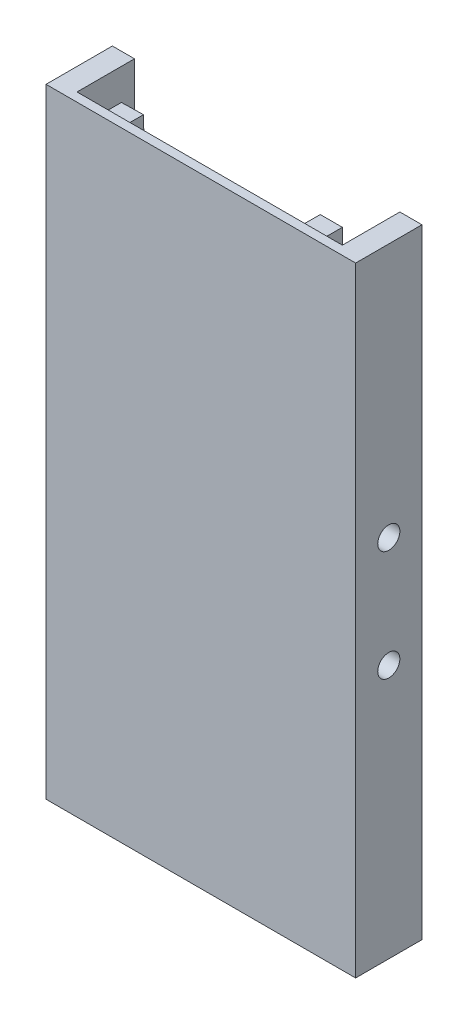
SolidWorks part; units mm, degrees
ref_plane "Front Plane" through (0, 0, 0) normal (0, 0, 1) x (1, 0, 0)
ref_plane "Top Plane" through (0, 0, 0) normal (0, 1, 0) x (1, 0, 0)
ref_plane "Right Plane" through (0, 0, 0) normal (1, 0, 0) x (0, 0, -1)
sketch "Sketch2" plane through (0, 0, 0) normal (0, 0, 1) x (1, 0, 0)
  line L0 (0, 438.8889) -> (0, 298.8889)
  line L1 (0, 298.8889) -> (70, 298.8889)
  line L2 (70, 298.8889) -> (70, 438.8889)
  line L4 (0, 438.8889) -> (70, 438.8889)
  dimension "D1" = 70
  dimension "D2" = 140
extrude "Boss-Extrude1" add sketch "Sketch2" against normal blind 15
sketch "Sketch3" plane through (0, 0, -15) normal (0, 0, -1) x (-1, 0, 0)
  line L0 (-65, 433.8889) -> (-65, 303.8889)
  line L1 (-65, 303.8889) -> (-5, 303.8889)
  line L2 (-5, 303.8889) -> (-5, 433.8889)
  line L4 (-65, 433.8889) -> (-5, 433.8889)
  line L5 (-70, 298.8889) -> (-70, 438.8889) construction
  line L6 (0, 438.8889) -> (0, 298.8889) construction
  line L7 (-70, 438.8889) -> (0, 438.8889) construction
  line L8 (0, 298.8889) -> (-70, 298.8889) construction
  dimension "D1" = 5
  dimension "D2" = 5
  dimension "D3" = 5
  dimension "D4" = 5
extrude "Cut-Extrude1" cut sketch "Sketch3" against normal blind 12.5
sketch "Sketch4" plane through (0, 438.8889, 0) normal (0, 1, 0) x (1, 0, 0)
  line L0 (5, 15) -> (5, 2)
  line L1 (5, 15) -> (65, 15)
  line L2 (65, 15) -> (65, 2)
  line L3 (65, 2) -> (5, 2)
  line L6 (70, 0) -> (0, 0) construction
  dimension "D1" = 2
extrude "Cut-Extrude2" cut sketch "Sketch4" against normal through all
sketch "Sketch7" plane through (0, 0, 0) normal (-1, 0, 0) x (0, 0, 1)
  line L0 (-7.5, 438.8889) -> (-7.5, 298.8889) construction
  line L1 (-15, 438.8889) -> (0, 438.8889) construction
  line L2 (-15, 298.8889) -> (0, 298.8889) construction
  line L3 (-25, 368.8889) -> (-15, 368.8889) construction
  line L4 (-15, 438.8889) -> (-15, 298.8889) construction
  circle A0 centre (-7.5, 381.3889) radius 2.5
  circle A1 centre (-7.5, 356.3889) radius 2.5
  dimension "D2" = 5
  dimension "D1" = 25
extrude "Cut-Extrude5" cut sketch "Sketch7" against normal through all
sketch "Sketch32" plane through (0, 298.8889, 0) normal (0, -1, 0) x (1, 0, 0)
  line L0 (35, -2) -> (35, 0) construction
  line L1 (5, -2) -> (65, -2) construction
  line L2 (0, 0) -> (70, 0) construction
  line L3 (33.5, -2) -> (36.5, -2)
  arc A0 (33.5, -2) -> (36.5, -2) centre (35, -2) cw
  dimension "D1" = 3
revolve "Cut-Revolve1" cut sketch "Sketch32" angle 30 about L3
ref_plane "Plane8" through (5, 0, 0) normal (1, 0, 0) x (0, 0, -1)
sketch "Sketch35" plane through (5, 0, 0) normal (1, 0, 0) x (0, 0, -1)
  circle A0 centre (7.5, 356.3889) radius 1
  dimension "D1" = 2
curve "Helix/Spiral6" pitch 1.5333 height 23 turns 15
ref_plane "Plane9" through (28, 355.6818, -8.2071) normal (0.2371, -0.6869, 0.6869) x (0.9715, 0.1676, -0.1676)
sketch "Sketch36" plane through (0, 0, -2) normal (0, 0, -1) x (-1, 0, 0)
  line L0 (-35, 438.8889) -> (-36.5, 298.8889) construction
  line L1 (-5, 438.8889) -> (-65, 438.8889) construction
  line L2 (-65, 368.8889) -> (-5, 368.8889) construction
  line L3 (-65, 438.8889) -> (-65, 298.8889) construction
  line L4 (-5, 298.8889) -> (-5, 438.8889) construction
  line L5 (-65, 298.8889) -> (-65, 438.8889) construction
  line L6 (-60, 437.3889) -> (-55, 437.3889)
  line L7 (-60, 437.3889) -> (-60, 432.3889)
  line L8 (-60, 432.3889) -> (-55, 432.3889)
  line L9 (-55, 437.3889) -> (-55, 432.3889)
  line L10 (-10.145, 431.8547) -> (-15.1439, 431.9619)
  line L11 (-10.0379, 436.8536) -> (-10.145, 431.8547)
  line L12 (-10.0379, 436.8536) -> (-15.0367, 436.9607)
  line L13 (-15.0367, 436.9607) -> (-15.1439, 431.9619)
  line L14 (-10.145, 305.923) -> (-15.1439, 305.8159)
  line L15 (-10.0379, 300.9242) -> (-10.145, 305.923)
  line L16 (-10.0379, 300.9242) -> (-15.0367, 300.8171)
  line L17 (-15.0367, 300.8171) -> (-15.1439, 305.8159)
  line L18 (-60, 305.3889) -> (-55, 305.3889)
  line L19 (-60, 300.3889) -> (-60, 305.3889)
  line L20 (-60, 300.3889) -> (-55, 300.3889)
  line L21 (-55, 300.3889) -> (-55, 305.3889)
  dimension "D1" = 5
  dimension "D2" = 5
  dimension "D3" = 5
  dimension "D4" = 5
  dimension "D5" = 1.5
extrude "Boss-Extrude2" add sketch "Sketch36" along normal blind 5
